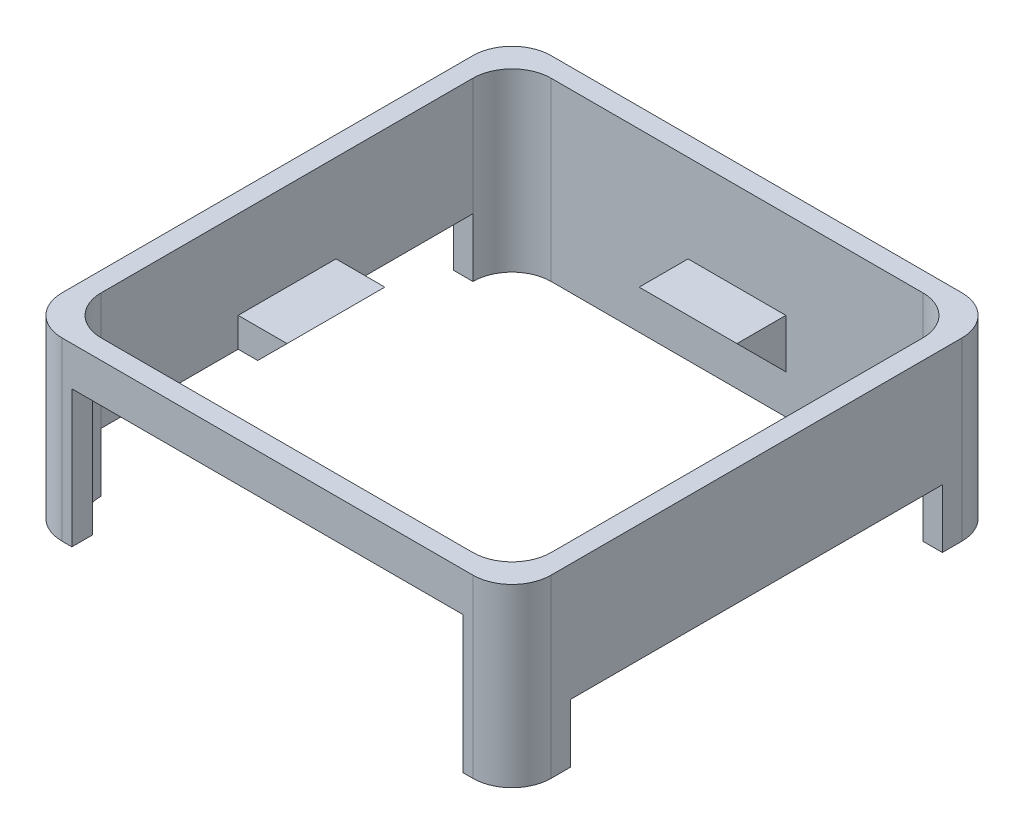
SolidWorks part; units mm, degrees
ref_plane "Front Plane" through (0, 0, 0) normal (0, 0, 1) x (1, 0, 0)
ref_plane "Top Plane" through (0, 0, 0) normal (0, 1, 0) x (1, 0, 0)
ref_plane "Right Plane" through (0, 0, 0) normal (1, 0, 0) x (0, 0, -1)
sketch "Sketch1" plane through (0, 0, 0) normal (0, 1, 0) x (1, 0, 0)
  line L1 (-125, -125) -> (125, -125)
  line L2 (-125, -125) -> (-125, 125)
  line L3 (-125, 125) -> (125, 125)
  line L4 (125, -125) -> (125, 125)
  line L5 (-115, -115) -> (115, -115)
  line L6 (-115, -115) -> (-115, 115)
  line L7 (-115, 115) -> (115, 115)
  line L8 (115, -115) -> (115, 115)
  line L9 (-115, -115) -> (115, 115) construction
  line L10 (-115, 115) -> (115, -115) construction
  point P0 (0, 0)
  point P6 (125, 0)
  point P7 (0, -125)
  point P8 (0, 0)
  dimension "D1" = 250
  dimension "D2" = 250
  dimension "D3" = 230
  dimension "D4" = 230
extrude "Boss-Extrude1" add sketch "Sketch1" along normal blind 90
sketch "Sketch2" plane through (0, 0, 125) normal (0, 0, 1) x (1, 0, 0)
  line L0 (-125, 0) -> (125, 0) construction
  line L1 (-100, 70) -> (100, 70)
  line L2 (-100, 70) -> (-100, 0)
  line L3 (-100, 0) -> (100, 0)
  line L4 (100, 70) -> (100, 0)
  line L6 (-125, 90) -> (125, 90) construction
  point P6 (0, 70)
  dimension "D1" = 200
  dimension "D2" = 20
extrude "Cut-Extrude1" cut sketch "Sketch2" against normal blind 50
fillet "Fillet1" radius 20 8 edges at (-115, 45, 115) (115, 45, 115) (115, 45, -115) (-115, 45, -115) (-125, 45, 125) (125, 45, 125) (125, 45, -125) (-125, 45, -125)
sketch "Sketch4" plane through (0, 0, 0) normal (0, 0, 1) x (1, 0, 0)
  line L0 (-115, 45) -> (-90, 45)
  line L1 (-90, 45) -> (-115, 20)
  line L2 (-115, 20) -> (-115, 45)
  line L3 (115, 45) -> (90, 45)
  line L4 (90, 45) -> (115, 20)
  line L5 (115, 20) -> (115, 45)
  line L8 (-105, 90) -> (-125, 90) construction
  line L9 (-125, 0) -> (-125, 90) construction
  line L10 (125, 90) -> (125, 0) construction
  point P12 (-115, 18.5034)
  dimension "D1" = 45
  dimension "D2" = 10
  dimension "D3" = 10
  dimension "D4" = 25
  dimension "D5" = 25
extrude "Boss-Extrude2" add sketch "Sketch4" along normal mid plane 50
sketch "Sketch5" plane through (0, 0, 0) normal (1, 0, 0) x (0, 0, -1)
  line L0 (115, 45) -> (115, 20)
  line L1 (115, 20) -> (90, 45)
  line L2 (90, 45) -> (115, 45)
  line L3 (-105, 90) -> (105, 90) construction
  line L4 (125, 90) -> (125, 0) construction
  dimension "D1" = 45
  dimension "D2" = 25
  dimension "D3" = 25
  dimension "D4" = 10
extrude "Boss-Extrude3" add sketch "Sketch5" along normal mid plane 50
sketch "Sketch6" plane through (125, 0, 0) normal (1, 0, 0) x (0, 0, -1)
  line L0 (-105, 0) -> (105, 0) construction
  line L1 (-95, 30) -> (95, 30)
  line L2 (-95, 30) -> (-95, 0)
  line L3 (-95, 0) -> (95, 0)
  line L4 (95, 30) -> (95, 0)
  line L6 (-125, 0) -> (-125, 90) construction
  line L7 (125, 90) -> (125, 0) construction
  dimension "D1" = 30
  dimension "D2" = 30
  dimension "D3" = 30
extrude "Cut-Extrude2" cut sketch "Sketch6" against normal through all
